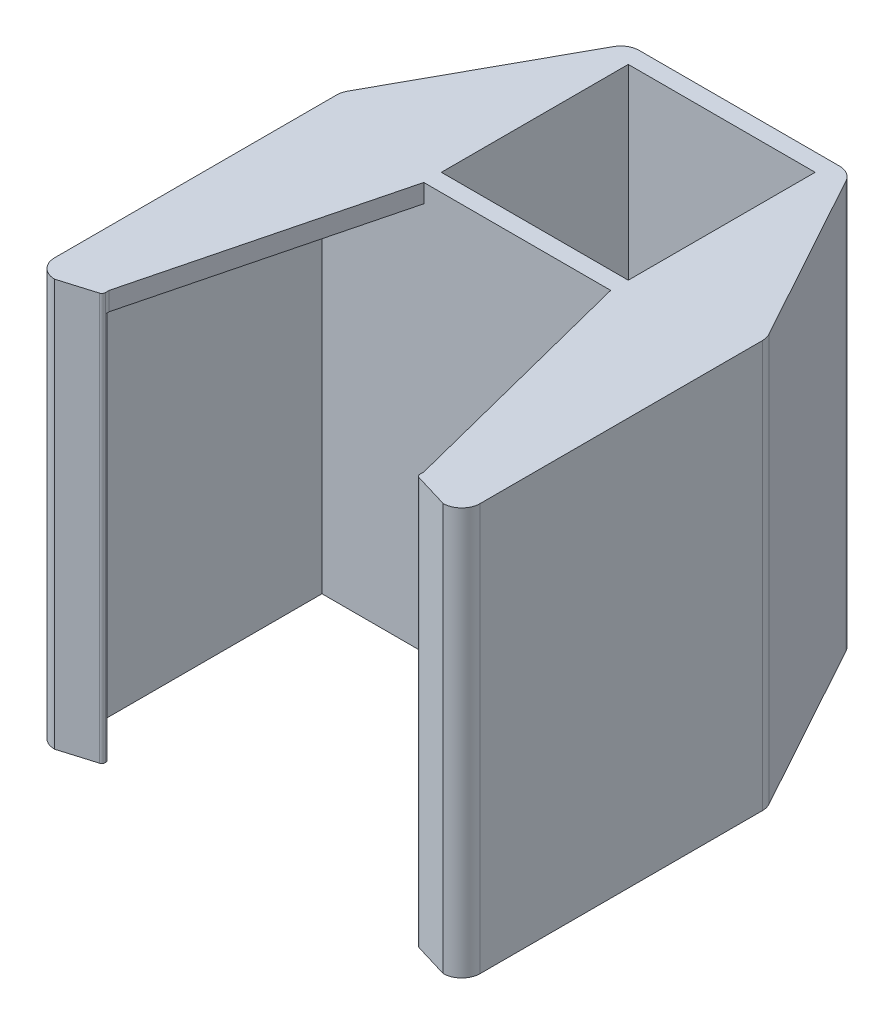
SolidWorks part; units mm, degrees
material "ABS"
ref_plane "Alzado" through (0, 0, 0) normal (0, 0, 1) x (1, 0, 0)
ref_plane "Planta" through (0, 0, 0) normal (0, 1, 0) x (1, 0, 0)
ref_plane "Vista lateral" through (0, 0, 0) normal (1, 0, 0) x (0, 0, -1)
ref_plane "Plano1" through (0, -115.9998, 0) normal (0, 1, 0) x (1, 0, 0)
sketch "Croquis1" plane through (0, -115.9998, 0) normal (0, 1, 0) x (1, 0, 0)
  line L0 (10.1, -331) -> (17, -358.1)
  line L1 (17, -358.1) -> (17, -358.8)
  line L2 (17, -358.8) -> (21, -360)
  line L3 (23, -358) -> (23, -327)
  line L4 (23, -327) -> (12, -307)
  line L5 (12, -307) -> (-12, -307)
  line L6 (-12, -307) -> (-23, -327)
  line L7 (-23, -327) -> (-23, -358)
  line L8 (-21, -360) -> (-17, -358.8)
  line L9 (-17, -358.8) -> (-17, -358.1)
  line L10 (-17, -358.1) -> (-10.1, -331)
  line L11 (-10.1, -331) -> (10.1, -331)
  arc A0 (21, -360) -> (23, -358) centre (21, -358) ccw
  arc A1 (-23, -358) -> (-21, -360) centre (-21, -358) ccw
extrude "Saliente-Extruir1" add sketch "Croquis1" against normal blind 2
sketch "Croquis2" plane through (0, -117.9998, 0) normal (0, -1, 0) x (1, 0, 0)
  line L0 (-17, 331) -> (17, 331)
  line L1 (17, 331) -> (17, 358.8)
  line L2 (17, 358.8) -> (21, 360)
  line L3 (23, 358) -> (23, 327)
  line L4 (23, 327) -> (12, 307)
  line L5 (12, 307) -> (-12, 307)
  line L6 (-12, 307) -> (-23, 327)
  line L7 (-23, 327) -> (-23, 358)
  line L8 (-21, 360) -> (-17, 358.8)
  line L9 (-17, 358.8) -> (-17, 331)
  arc A0 (21, 360) -> (23, 358) centre (21, 358) cw
  arc A1 (-23, 358) -> (-21, 360) centre (-21, 358) cw
extrude "Saliente-Extruir2" add sketch "Croquis2" along normal blind 42
ref_plane "Plano2" through (-21.1, 0, 0) normal (-1, 0, 0) x (0, -1, 0)
sketch "Croquis3" plane through (-21.1, 0, 0) normal (-1, 0, 0) x (0, -1, 0)
  line L0 (117.9998, 358.1) -> (117.9998, 331)
  line L1 (117.9998, 331) -> (159.9998, 331)
  line L2 (159.9998, 331) -> (159.9998, 358.1)
  line L3 (159.9998, 358.1) -> (117.9998, 358.1)
extrude "Cortar-Extruir1" cut sketch "Croquis3" against normal up to next
ref_plane "Plano3" through (21.1, 0, 0) normal (1, 0, 0) x (0, 0, -1)
sketch "Croquis4" plane through (21.1, 0, 0) normal (1, 0, 0) x (0, 0, -1)
  line L0 (-331, -117.9998) -> (-358.1, -117.9998)
  line L1 (-358.1, -117.9998) -> (-358.1, -159.9998)
  line L2 (-358.1, -159.9998) -> (-331, -159.9998)
  line L3 (-331, -159.9998) -> (-331, -117.9998)
extrude "Cortar-Extruir2" cut sketch "Croquis4" against normal up to next
sketch "Croquis5" plane through (0, -115.9998, 0) normal (0, 1, 0) x (-1, 0, 0)
  line L0 (10.1, 329.1) -> (-10.1, 329.1)
  line L1 (-10.1, 329.1) -> (-10.1, 308.9)
  line L2 (-10.1, 308.9) -> (10.1, 308.9)
  line L3 (10.1, 308.9) -> (10.1, 329.1)
extrude "Cortar-Extruir3" cut sketch "Croquis5" against normal through all
hole_wizard "Diámetro de taladro Ø4.2 (4.2)1" positions "Croquis7" profile "Croquis6" hole size "Ø4.2" standard "Ansi Metric"
sketch "Croquis7" plane through (0, 0, 307) normal (0, 0, -1) x (-1, 0, 0)
  point P0 (0, -137.9998)
sketch "Croquis6" plane through (0, -137.9998, 307) normal (1, 0, 0) x (0, 1, 0)
  line L0 (0, 0) -> (0, 1.9)
  line L1 (0, 1.9) -> (2.1, 1.9)
  line L2 (2.1, 1.9) -> (2.1, 0)
  line L5 (2.1, 0) -> (0, 0)
  line L11 (0, -6.35) -> (0, 107.95) construction
  dimension "Diámetro de taladro hasta el siguiente" = 4.2
  dimension "Profundidad de taladro hasta el siguiente" = 1.9
fillet "Redondeo1" radius 0.4 4 edges at (17, -138.9998, 358.1) (17, -137.9998, 358.8) (-17, -138.9998, 358.1) (-17, -137.9998, 358.8)
fillet "Redondeo2" radius 1.9 2 edges at (21.1, -138.9998, 358.1) (-21.1, -138.9998, 358.1)
fillet "Redondeo3" radius 2 4 edges at (-12, -137.9998, 307) (23, -137.9998, 327) (12, -137.9998, 307) (-23, -137.9998, 327)
